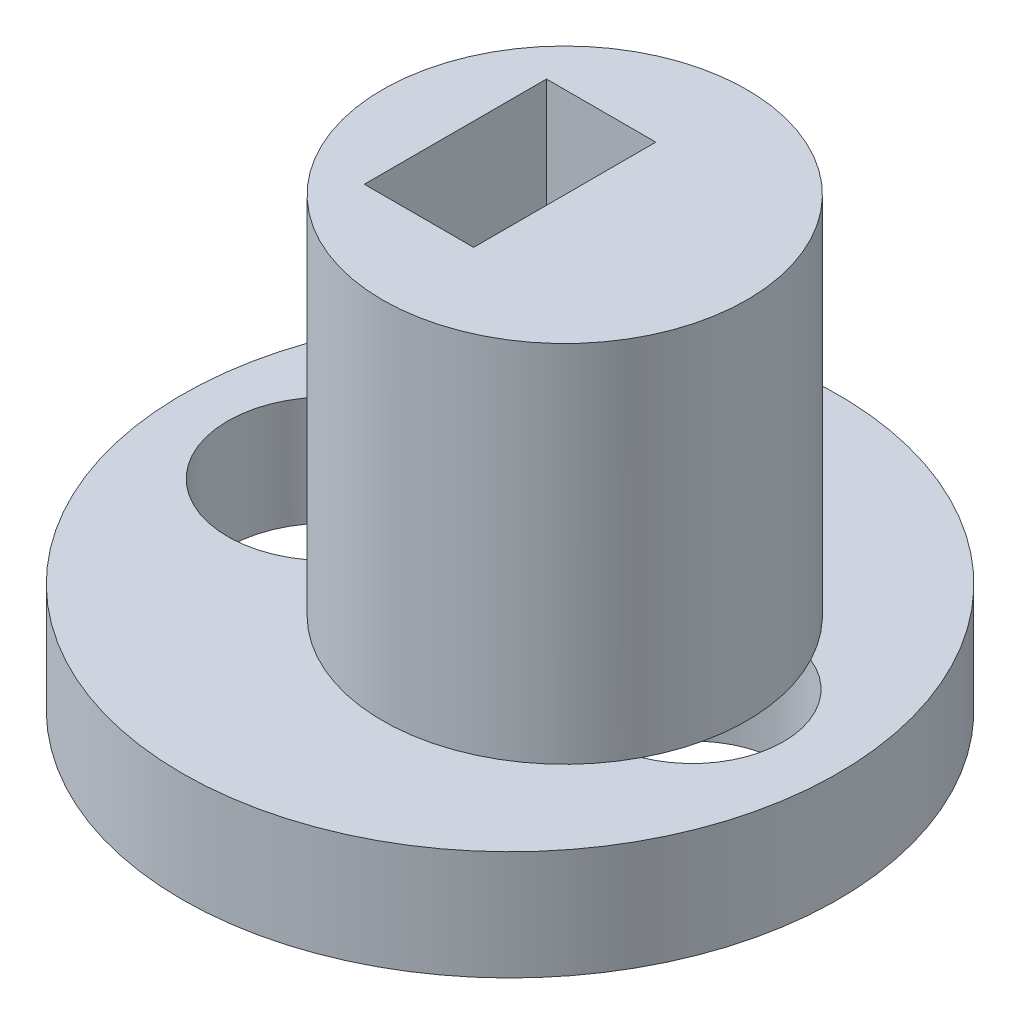
SolidWorks part; units mm, degrees
ref_plane "Front Plane" through (0, 0, 0) normal (0, 0, 1) x (1, 0, 0)
ref_plane "Top Plane" through (0, 0, 0) normal (0, 1, 0) x (1, 0, 0)
ref_plane "Right Plane" through (0, 0, 0) normal (1, 0, 0) x (0, 0, -1)
sketch "Sketch1" plane through (0, 0, 0) normal (0, 1, 0) x (1, 0, 0)
  circle A1 centre (-5, 0.0008) radius 2.75
  circle A2 centre (0, 0) radius 9
  circle A3 centre (5, 0) radius 2.5
  dimension "D1" = 18
  dimension "D3" = 5.5
  dimension "D4" = 5
  dimension "D2" = 5
  dimension "D5" = 5
extrude "Boss-Extrude1" add sketch "Sketch1" along normal blind 3
sketch "Sketch4" plane through (0, 3, 0) normal (0, 1, 0) x (1, 0, 0)
  line L2 (-1.5, 2.5) -> (-1.5, -2.5)
  line L3 (1.5, -2.5) -> (1.5, 2.5)
  line L6 (1.5, 2.5) -> (-1.5, 2.5)
  line L7 (-1.5, -2.5) -> (1.5, -2.5)
  circle A0 centre (1.5, 0) radius 5
  dimension "D2" = 10
  dimension "D1" = 1.5
extrude "Boss-Extrude4" add sketch "Sketch4" along normal blind 10
sketch "Sketch5" plane through (0, 0, 0) normal (0, -1, 0) x (1, 0, 0)
  circle A0 centre (5, 0) radius 2.5 construction
  circle A1 centre (0, 0) radius 9
  circle A2 centre (0, 0) radius 9
  circle A3 centre (-5, -0.0008) radius 2.75 construction
  circle A4 centre (5, 0) radius 2.5
  circle A5 centre (-5, -0.0008) radius 2.75
  dimension "D1" = 0
